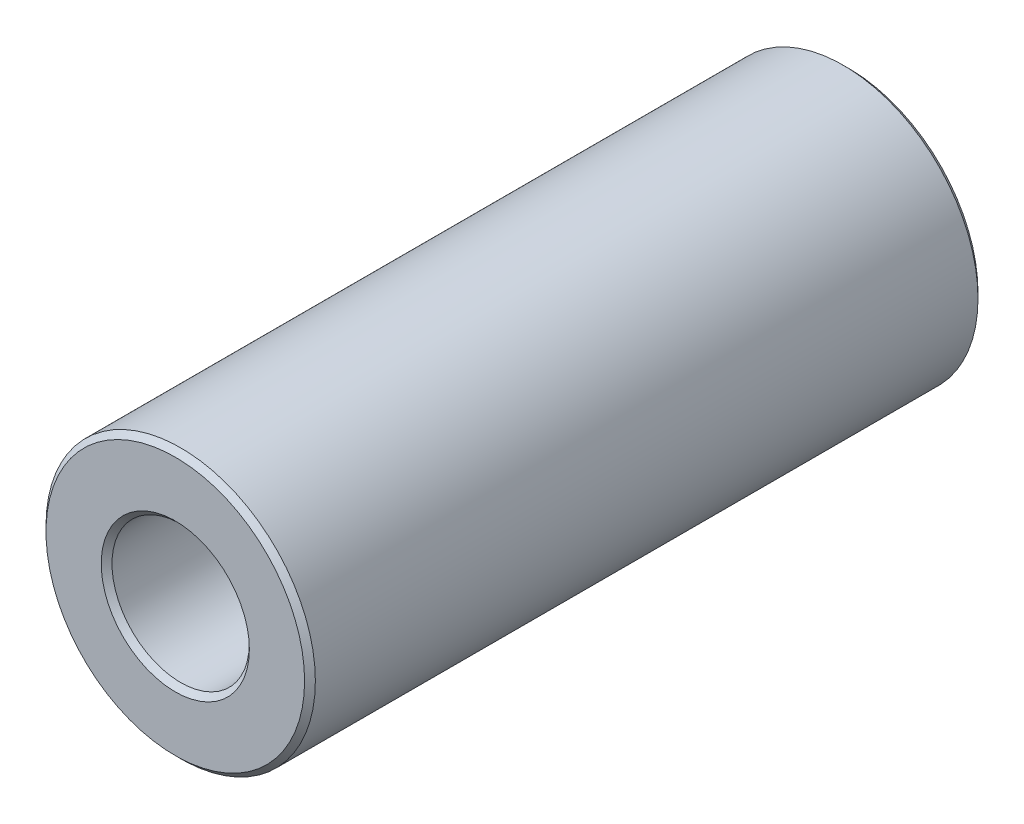
SolidWorks part; units mm, degrees
material "6061-T6 (SS)"
ref_plane "Front Plane" through (0, 0, 0) normal (0, 0, 1) x (1, 0, 0)
ref_plane "Top Plane" through (0, 0, 0) normal (0, 1, 0) x (1, 0, 0)
ref_plane "Right Plane" through (0, 0, 0) normal (1, 0, 0) x (0, 0, -1)
sketch "Sketch1" plane through (0, 0, 0) normal (0, 0, 1) x (1, 0, 0)
  circle A0 centre (0, 0) radius 2.55
  circle A1 centre (0, 0) radius 5
  dimension "D1" = 5.1
  dimension "D2" = 10
extrude "Boss-Extrude1" add sketch "Sketch1" along normal blind 25
chamfer "Chamfer1" distance 0.2 angle 45 4 edges at (5, 0, 0) (2.55, 0, 0) (2.55, 0, 25) (5, 0, 25)
